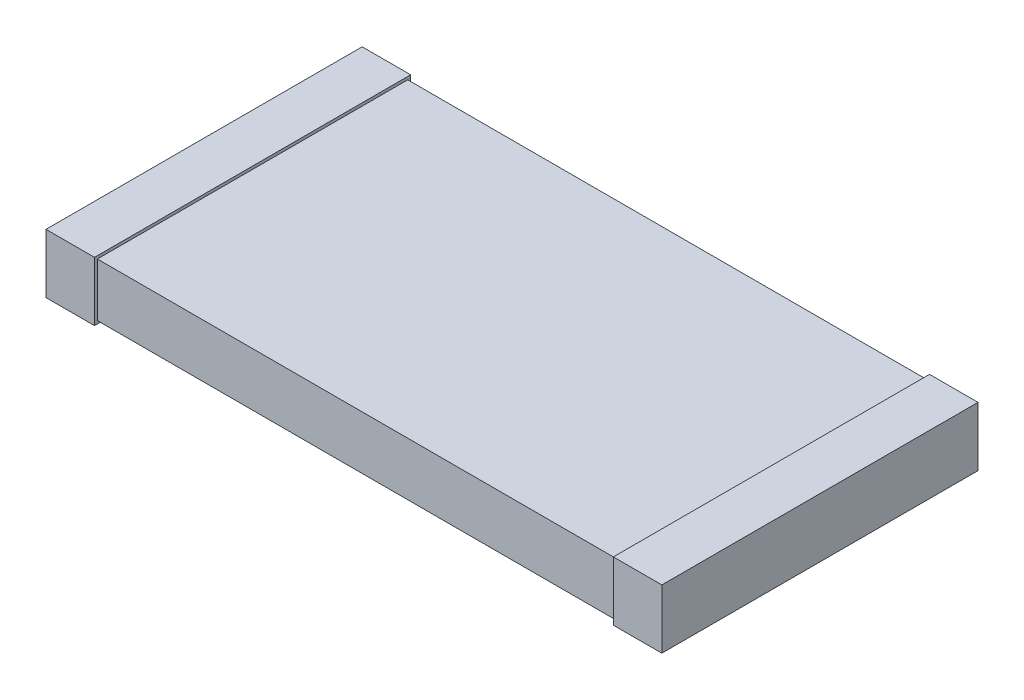
SolidWorks part; units mm, degrees
ref_plane "Front Plane" through (0, 0, 0) normal (0, 0, 1) x (1, 0, 0)
ref_plane "Top Plane" through (0, 0, 0) normal (0, 1, 0) x (1, 0, 0)
ref_plane "Right Plane" through (0, 0, 0) normal (1, 0, 0) x (0, 0, -1)
sketch "Sketch1" plane through (0, 0, 0) normal (0, 1, 0) x (1, 0, 0)
  line L1 (-3.175, 1.6) -> (3.175, 1.6)
  line L2 (-3.175, 1.6) -> (-3.175, -1.6)
  line L3 (-3.175, -1.6) -> (3.175, -1.6)
  line L4 (3.175, 1.6) -> (3.175, -1.6)
  point P4 (0, 1.6)
  point P6 (3.175, 0)
  dimension "D1" = 3.2
  dimension "D2" = 6.35
extrude "Extrude1" add sketch "Sketch1" along normal blind 0.55
sketch "Sketch2" plane through (0, 0, 0) normal (0, 0, 1) x (1, 0, 0)
  line L0 (-3.175, 0.55) -> (-3.175, 0) construction
  line L1 (-2.675, 0.58) -> (-3.175, 0.58)
  line L2 (-2.675, 0.58) -> (-2.675, -0.03)
  line L3 (-2.675, -0.03) -> (-3.175, -0.03)
  line L4 (-3.175, 0.58) -> (-3.175, -0.03)
  line L5 (-3.175, 0.55) -> (3.175, 0.55) construction
  line L6 (-3.175, 0) -> (3.175, 0) construction
  line L7 (0, 0) -> (0, -0.3575) construction
  line L8 (3.175, 0.58) -> (3.175, -0.03)
  line L9 (2.675, -0.03) -> (3.175, -0.03)
  line L10 (2.675, 0.58) -> (2.675, -0.03)
  line L11 (2.675, 0.58) -> (3.175, 0.58)
  dimension "D1" = 0.5
  dimension "D2" = 0.03
  dimension "D3" = 0.03
extrude "Extrude2" add sketch "Sketch2" along normal offset from surface 0.03 and the other way offset from surface (1.63 mm away) 0.03 up to face at (0, 0.275, 1.6) offset beyond the face yes other way up to face at (0, 0.275, -1.6)
ref_plane "Board Surface" through (0, -0.03, 0) normal (0, 1, 0) x (-1, 0, 0)
sketch "Component_Outline" plane through (0, -0.03, 0) normal (0, 1, 0) x (-1, 0, 0)
  line L0 (3.175, 1.63) -> (2.675, 1.63)
  line L1 (2.675, 1.63) -> (2.675, 1.6)
  line L2 (2.675, 1.6) -> (-2.675, 1.6)
  line L3 (-2.675, 1.63) -> (-3.175, 1.63)
  line L4 (3.175, 1.63) -> (3.175, -1.63)
  line L5 (3.175, -1.63) -> (2.675, -1.63)
  line L6 (2.675, -1.63) -> (2.675, -1.6)
  line L7 (2.675, -1.6) -> (-2.675, -1.6)
  line L8 (-2.675, -1.6) -> (-2.675, -1.63)
  line L9 (-2.675, -1.63) -> (-3.175, -1.63)
  line L10 (-3.175, -1.63) -> (-3.175, 1.63)
  arc A0 (-2.675, 1.6) -> (-2.675, 1.63) centre (-2.675, 1.615) cw
  point P15 (0, 0)
